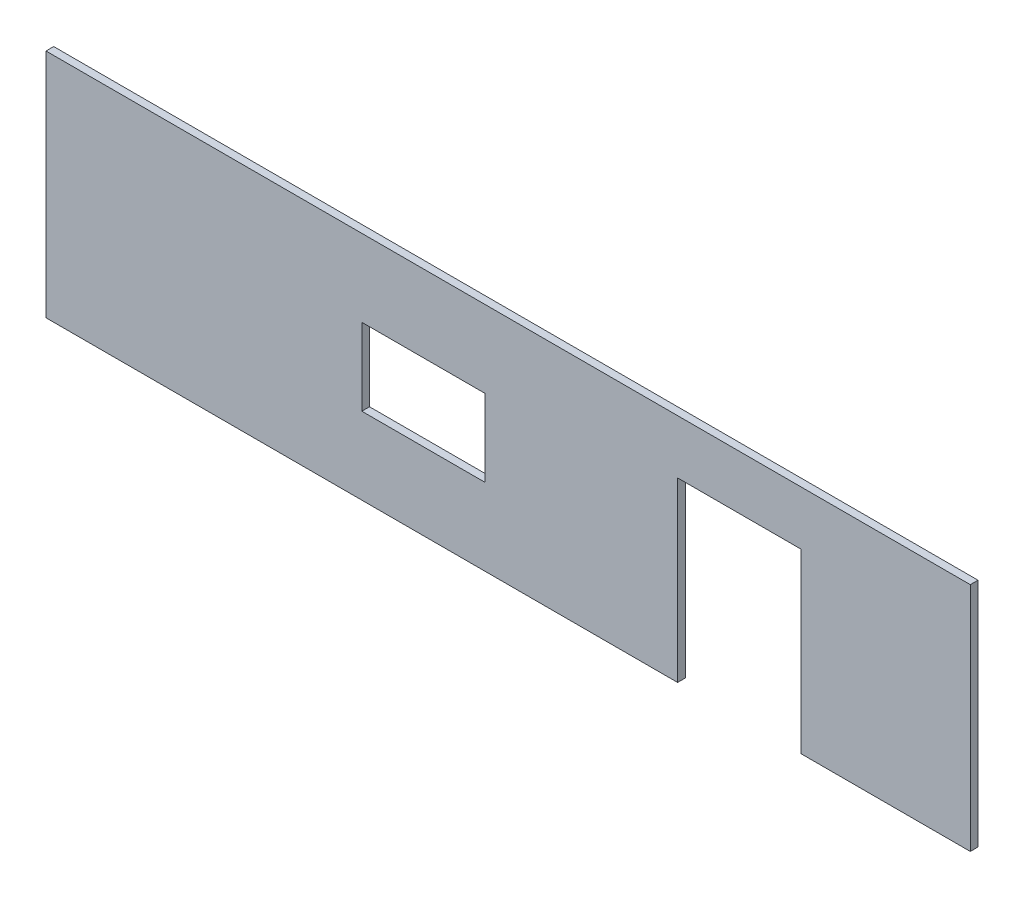
SolidWorks part; units mm, degrees
ref_plane "Front Plane" through (0, 0, 0) normal (0, 0, 1) x (1, 0, 0)
ref_plane "Top Plane" through (0, 0, 0) normal (0, 1, 0) x (1, 0, 0)
ref_plane "Right Plane" through (0, 0, 0) normal (1, 0, 0) x (0, 0, -1)
sketch "Sketch1" plane through (0, 0, 0) normal (0, 0, 1) x (1, 0, 0)
  line L0 (-130, 75) -> (-130, -75) construction
  line L1 (-300, 75) -> (300, 75)
  line L2 (-300, 75) -> (-300, -75)
  line L3 (-300, -75) -> (110, -75)
  line L4 (300, 75) -> (300, -75)
  line L5 (-300, 75) -> (300, -75) construction
  line L6 (-300, -75) -> (300, 75) construction
  line L11 (190, -75) -> (190, 40)
  line L12 (-95, 25) -> (-15, 25)
  line L13 (-95, 25) -> (-95, -25)
  line L18 (-95, -25) -> (-15, -25)
  line L19 (-15, 25) -> (-15, -25)
  line L20 (-95, 25) -> (-15, -25) construction
  line L21 (-95, -25) -> (-15, 25) construction
  line L22 (110, 40) -> (110, -75)
  line L23 (110, 40) -> (190, 40)
  line L24 (190, -75) -> (300, -75)
  point P0 (0, 0)
  point P9 (-55, 0)
  point P15 (0, 0)
  point P18 (150, 40)
  dimension "D1" = 600
  dimension "D2" = 150
  dimension "D3" = 80
  dimension "D4" = 170
  dimension "D5" = 50
  dimension "D6" = 75
  dimension "D7" = 75
  dimension "D8" = 80
  dimension "D9" = 150
  dimension "D10" = 115
extrude "Boss-Extrude1" add sketch "Sketch1" along normal blind 5
